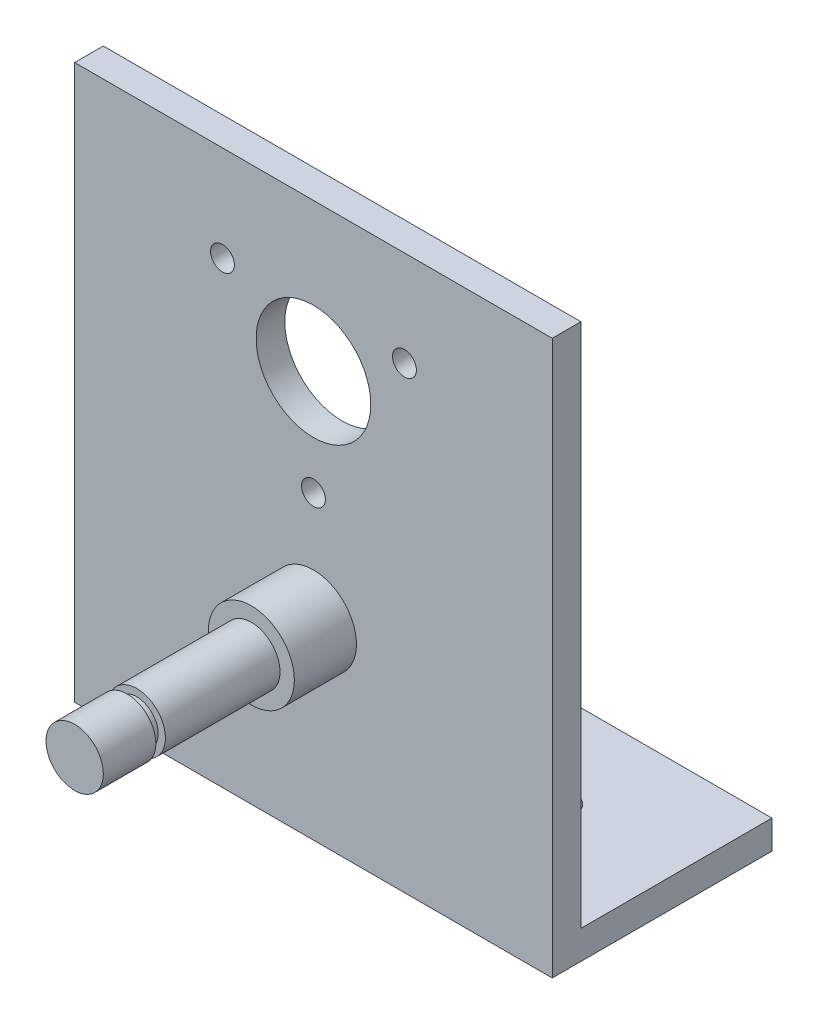
SolidWorks part; units mm, degrees
ref_plane "Front Plane" through (0, 0, 0) normal (0, 0, 1) x (1, 0, 0)
ref_plane "Top Plane" through (0, 0, 0) normal (0, 1, 0) x (1, 0, 0)
ref_plane "Right Plane" through (0, 0, 0) normal (1, 0, 0) x (0, 0, -1)
sketch "Sketch1" plane through (0, 0, 0) normal (0, 0, 1) x (1, 0, 0)
  line L1 (-55.6197, -21.4873) -> (-5.6197, -21.4873)
  line L2 (-55.6197, -21.4873) -> (-55.6197, 36.5127)
  line L3 (-55.6197, 36.5127) -> (-5.6197, 36.5127)
  line L4 (-5.6197, -21.4873) -> (-5.6197, 36.5127)
  dimension "D1" = 50
  dimension "D2" = 58
extrude "Boss-Extrude1" add sketch "Sketch1" along normal blind 3
sketch "Sketch2" plane through (0, 0, 0) normal (0, 0, -1) x (-1, 0, 0)
  line L0 (55.6197, 36.5127) -> (55.6197, -21.4873) construction
  line L1 (5.6197, -21.4873) -> (55.6197, -21.4873)
  line L2 (5.6197, -21.4873) -> (5.6197, -18.4873)
  line L3 (5.6197, -18.4873) -> (55.6197, -18.4873)
  line L4 (55.6197, -21.4873) -> (55.6197, -18.4873)
  dimension "D1" = 3
extrude "Boss-Extrude2" add sketch "Sketch2" along normal blind 20
sketch "Sketch4" plane through (0, -21.4873, 0) normal (0, -1, 0) x (-1, 0, 0)
  line L0 (30.6197, -3) -> (30.6197, 20) construction
  line L1 (55.6197, -3) -> (5.6197, -3) construction
  line L2 (5.6197, 20) -> (55.6197, 20) construction
sketch "Sketch6" plane through (0, 0, 3) normal (0, 0, 1) x (1, 0, 0)
  line L0 (-55.6197, -21.4873) -> (-5.6197, -21.4873) construction
  circle A0 centre (-30.6197, -1.4873) radius 3
  dimension "D1" = 20
extrude "Boss-Extrude3" add sketch "Sketch6" along normal blind 25
sketch "Sketch7" plane through (0, 0, 3) normal (0, 0, 1) x (1, 0, 0)
  circle A0 centre (-30.6197, 21.0127) radius 6
  circle A1 centre (-30.6197, -1.4873) radius 3 construction
  dimension "D1" = 22.5
extrude "Cut-Extrude2" cut sketch "Sketch7" against normal through all
sketch "Sketch9" plane through (0, -18.4873, 0) normal (0, 1, 0) x (1, 0, 0)
  line L0 (-55.6197, 20) -> (-5.6197, 20) construction
  line L1 (-5.6197, 20) -> (-5.6197, 0) construction
  line L2 (-55.6197, 20) -> (-55.6197, 0) construction
  circle A0 centre (-18.1197, 10) radius 1.9
  circle A1 centre (-43.1197, 10) radius 1.9
  dimension "D1" = 10
  dimension "D2" = 10
  dimension "D3" = 12.5
  dimension "D4" = 12.5
extrude "Cut-Extrude3" cut sketch "Sketch9" against normal through all
sketch "Sketch10" plane through (0, 0, 3) normal (0, 0, 1) x (1, 0, 0)
  line L0 (-30.6197, 21.0127) -> (-30.6197, 10.0127) construction
  line L1 (-30.6197, 21.0127) -> (-21.0934, 26.5127) construction
  line L2 (-30.6197, 21.0127) -> (-40.146, 26.5127) construction
  circle A0 centre (-40.146, 26.5127) radius 1.25
  circle A1 centre (-21.0934, 26.5127) radius 1.25
  circle A2 centre (-30.6197, 10.0127) radius 1.25
extrude "Cut-Extrude4" cut sketch "Sketch10" against normal blind 10
ref_plane "Plane1" through (0, 0, 9.5) normal (0, 0, 1) x (1, 0, 0)
sketch "Sketch11" plane through (0, 0, 9.5) normal (0, 0, 1) x (1, 0, 0)
  circle A0 centre (-30.6197, -1.4873) radius 4.5
extrude "Boss-Extrude4" add sketch "Sketch11" against normal up to next
ref_plane "Plane2" through (0, 0, 21.5) normal (0, 0, 1) x (1, 0, 0)
sketch "Sketch12" plane through (0, 0, 21.5) normal (0, 0, 1) x (1, 0, 0)
  circle A0 centre (-30.6197, -1.4873) radius 3
  circle A1 centre (-30.6197, -1.4873) radius 2.25
  dimension "D1" = 0.75
extrude "Cut-Extrude5" cut sketch "Sketch12" along normal blind 1
